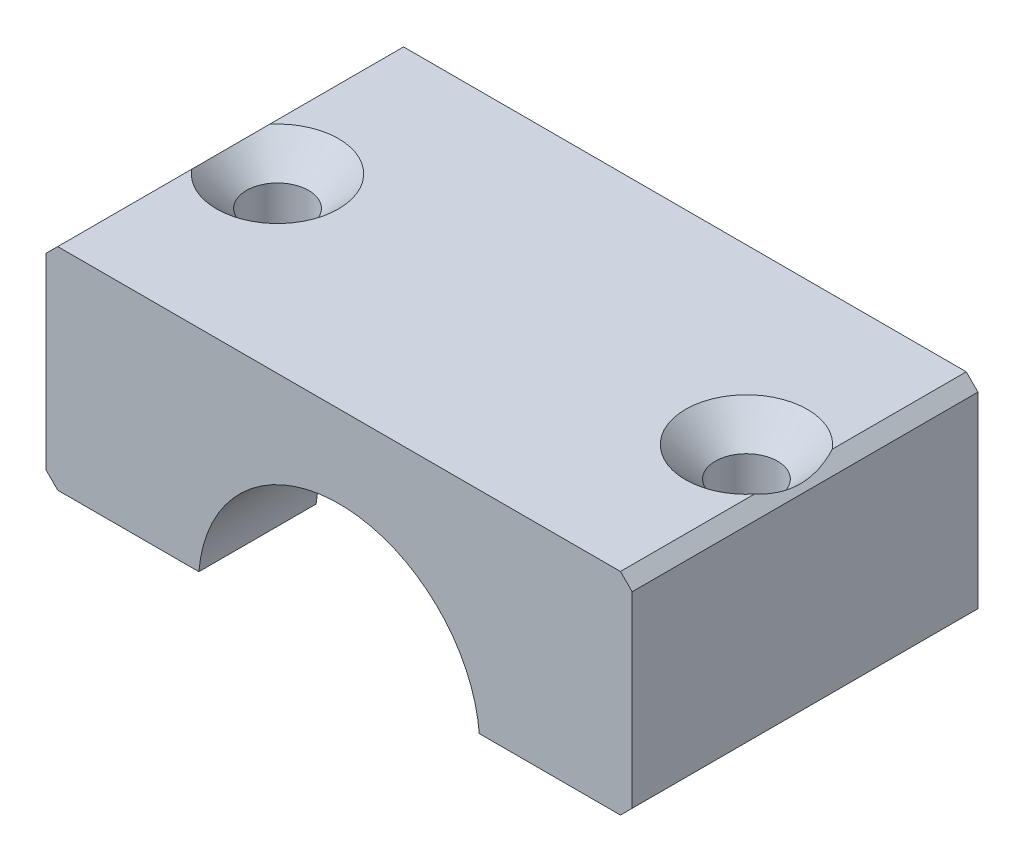
SolidWorks part; units mm, degrees
material "Латунь"
ref_plane "Front" through (0, 0, 0) normal (0, 0, 1) x (1, 0, 0)
ref_plane "Top" through (0, 0, 0) normal (0, 1, 0) x (1, 0, 0)
ref_plane "Right" through (0, 0, 0) normal (1, 0, 0) x (0, 0, -1)
sketch "Sketch2" plane through (0, 0, 0) normal (0, 0, 1) x (1, 0, 0)
  line L0 (11.9583, 1) -> (25, 1)
  line L1 (-25, 1) -> (-11.9583, 1)
  line L2 (-25, 1) -> (-25, 19)
  line L3 (-25, 19) -> (25, 19)
  line L4 (25, 1) -> (25, 19)
  arc A0 (11.9583, 1) -> (-11.9583, 1) centre (0, 0) ccw
  point P4 (-11.8929, 1.6)
  point P5 (11.9583, 1)
  point P6 (-25, 1)
  dimension "D1" = 12
  dimension "D2" = 50
  dimension "D3" = 18
  dimension "D4" = 1
extrude "Boss-Extrude1" add sketch "Sketch2" along normal blind 29.5
chamfer "Chamfer1" distance 1 distance2 1 4 edges at (-25, 19, 14.75) (-25, 1, 14.75) (25, 1, 14.75) (25, 19, 14.75)
ref_plane "Plane1" through (0, 0, 0) normal (0, -1, 0) x (-1, 0, 0)
sketch "Sketch4" plane through (0, 0, 0) normal (0, -1, 0) x (-1, 0, 0)
  line L0 (0, 0) -> (0, -29.5) construction
  line L3 (4.2094, -10) -> (15, -10)
  line L4 (4.2094, -10) -> (4.2094, -19.5)
  line L5 (4.2094, -19.5) -> (15, -19.5)
  line L6 (15, -10) -> (15, -19.5)
  line L9 (-11.9583, -29.5) -> (-24, -29.5) construction
  point P3 (0, -14.75)
  point P4 (4.2094, -14.75)
  dimension "D1" = 9.5
  dimension "D3" = 15
revolve "Cut-Revolve1" cut sketch "Sketch4" angle 360 about L0
ref_plane "Plane2" through (0, 19, 0) normal (0, 1, 0) x (1, 0, 0)
sketch "Sketch5" plane through (0, 19, 0) normal (0, -1, 0) x (1, 0, 0)
  line L4 (-20, 14.75) -> (20, 14.75) construction
  point P16 (-20, 14.75)
  point P17 (20, 14.75)
  point P18 (0, 14.75)
hole_wizard "Зенковка для  винта с плоской головкой M51" positions "Sketch9" profile "Sketch8" countersink size "M5" standard "Ansi Metric" end condition through all
sketch "Sketch9" plane through (0, 19, 0) normal (0, 1, 0) x (1, 0, 0)
  point P0 (-20, -14.75)
  point P3 (20, -14.75)
sketch "Sketch8" plane through (-20, 19, 14.75) normal (1, 0, 0) x (0, 0, 1)
  line L0 (0, 0) -> (0, 18)
  line L1 (0, 18) -> (2.65, 18)
  line L2 (2.65, 18) -> (2.65, 2.55)
  line L3 (2.65, 2.55) -> (5.2, 0)
  line L5 (5.2, 0) -> (0, 0)
  line L6 (-2.65, 2.55) -> (-5.2, 0) construction
  line L11 (0, -6.35) -> (0, 107.95) construction
  dimension "Thru Hole Dia." = 5.3
  dimension "Thru Hole Depth" = 18
  dimension "Near C'Sink Dia." = 10.4
  dimension "Near C'Sink Angle" = 90
